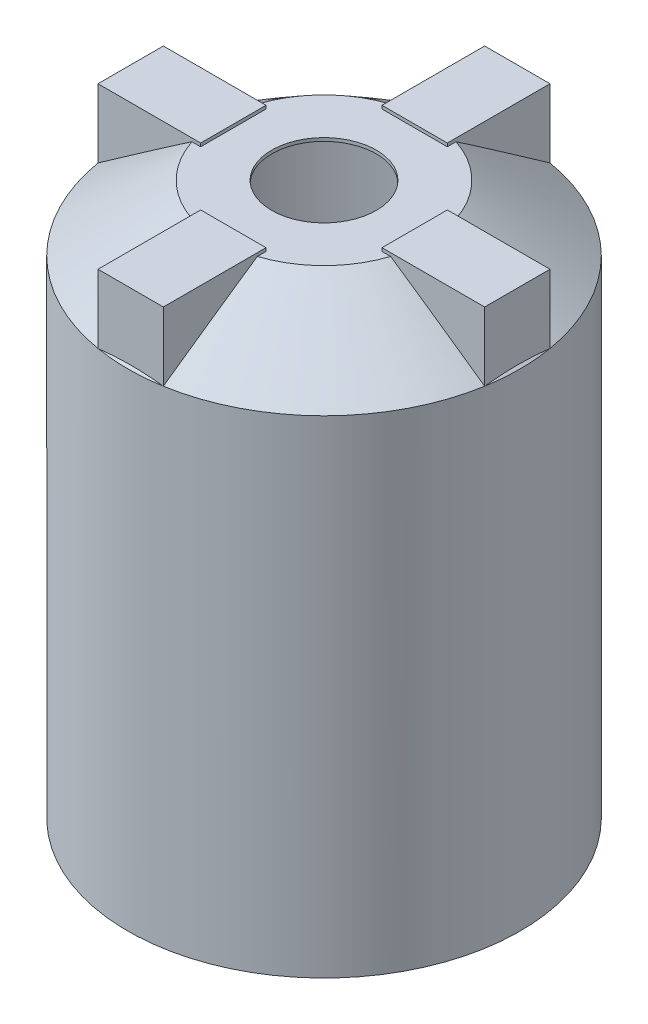
SolidWorks part; units mm, degrees
material "Polyethylene Cross-Linked"
ref_plane "Front Plane" through (0, 0, 0) normal (0, 0, 1) x (1, 0, 0)
ref_plane "Top Plane" through (0, 0, 0) normal (0, 1, 0) x (1, 0, 0)
ref_plane "Right Plane" through (0, 0, 0) normal (1, 0, 0) x (0, 0, -1)
sketch "Sketch1" plane through (0, 0, 0) normal (0, 1, 0) x (1, 0, 0)
  circle A0 centre (0, 0) radius 381
  circle A1 centre (0, 0) radius 374.65
  dimension "D1" = 762
  dimension "D2" = 6.35
extrude "Boss-Extrude1" add sketch "Sketch1" along normal blind 1066.8
sketch "Sketch3" plane through (0, 0, 0) normal (0, 0, 1) x (1, 0, 0)
  line L0 (0, 1066.8) -> (0, 0) construction
  line L2 (203.2, 1066.8) -> (381, 939.8)
  line L3 (381, 1066.8) -> (-381, 1066.8) construction
  line L4 (381, 0) -> (381, 1066.8) construction
  line L8 (374.65, 1066.8) -> (-374.65, 1066.8) construction
  line L9 (201.165, 1060.45) -> (381, 931.9965)
  line L10 (381, 931.9965) -> (381, 939.8)
  line L11 (101.6, 1066.8) -> (101.6, 1060.45)
  line L12 (101.6, 1060.45) -> (201.165, 1060.45)
  line L13 (101.6, 1066.8) -> (203.2, 1066.8)
  point P3 (0, 0)
  point P4 (0, 0)
  point P21 (101.5243, 1066.8)
  dimension "D1" = 203.2
  dimension "D2" = 127
  dimension "D3" = 6.35
  dimension "D4" = 101.6
  dimension "D5" = 6.35
sketch "Sketch4" plane through (0, 1066.8, 0) normal (0, 1, 0) x (1, 0, 0)
  line L0 (63.5, -172.4711) -> (-63.5, -172.4711)
  line L1 (172.4711, 63.5) -> (375.6711, 63.5)
  line L2 (172.4711, 63.5) -> (172.4711, -63.5)
  line L3 (172.4711, -63.5) -> (375.6711, -63.5)
  line L4 (375.6711, 63.5) -> (375.6711, -63.5)
  line L5 (172.4711, 63.5) -> (375.6711, -63.5) construction
  line L6 (172.4711, -63.5) -> (375.6711, 63.5) construction
  line L7 (63.5, -172.4711) -> (63.5, -375.6711)
  line L8 (63.5, -375.6711) -> (-63.5, -375.6711)
  line L9 (-63.5, -172.4711) -> (-63.5, -375.6711)
  line L10 (-172.4711, -63.5) -> (-172.4711, 63.5)
  line L11 (-172.4711, -63.5) -> (-375.6711, -63.5)
  line L12 (-375.6711, -63.5) -> (-375.6711, 63.5)
  line L13 (-172.4711, 63.5) -> (-375.6711, 63.5)
  line L14 (-63.5, 172.4711) -> (63.5, 172.4711)
  line L15 (-63.5, 172.4711) -> (-63.5, 375.6711)
  line L16 (-63.5, 375.6711) -> (63.5, 375.6711)
  line L17 (63.5, 172.4711) -> (63.5, 375.6711)
  circle A2 centre (0, 0) radius 381 construction
  point P0 (274.0711, 0)
  point P5 (0, 0)
  point P6 (-125.3542, -202.3243)
  point P7 (0, 0)
  point P8 (0, 0)
  point P12 (0, 0)
  point P24 (0, 0)
  point P25 (62.648, -375.8141)
  point P26 (-59.9828, 357.5468)
  point P27 (-375.6639, 63.5422)
  point P28 (63.5, -178.9101)
  dimension "D1" = 127
  dimension "D3" = 203.2
  dimension "D2" = 4
revolve "Revolve1" add sketch "Sketch3" angle 360 about L0
sketch "Sketch5" plane through (0, 0, 0) normal (0, 0, 1) x (1, 0, 0)
  line L0 (203.2, 1066.8) -> (381, 939.8)
  line L1 (172.4711, 1066.8) -> (375.6711, 1066.8) construction
  line L2 (203.2, 1066.8) -> (-203.2, 1066.8) construction
  line L3 (381, 0) -> (381, 1066.8) construction
  line L4 (381, 939.8) -> (381, 1066.8)
  line L5 (381, 1066.8) -> (203.2, 1066.8)
  line L6 (0, 0) -> (0, 1066.8) construction
  dimension "D1" = 177.8
  dimension "D2" = 127
revolve "Cut-Revolve2" cut sketch "Sketch5" angle 360 about L6
extrude "Cut-Extrude7" cut sketch "Sketch4" against normal blind 127
sketch "Sketch6" plane through (0, 1066.8, 0) normal (0, 1, 0) x (1, 0, 0)
  line L0 (172.4711, 63.5) -> (172.4711, -63.5) construction
  line L1 (172.4711, 63.5) -> (375.6711, 63.5)
  line L2 (172.4711, 63.5) -> (172.4711, -63.5)
  line L3 (172.4711, -63.5) -> (375.6711, -63.5)
  line L4 (375.6711, 63.5) -> (375.6711, -63.5)
  line L5 (172.4711, 63.5) -> (375.6711, -63.5) construction
  line L6 (172.4711, -63.5) -> (375.6711, 63.5) construction
  line L10 (63.5, -172.4711) -> (-63.5, -172.4711)
  line L11 (182.5176, 57.2209) -> (365.6245, 57.2209)
  line L12 (182.5176, 57.2209) -> (182.5176, -57.2209)
  line L13 (182.5176, -57.2209) -> (365.6245, -57.2209)
  line L14 (365.6245, 57.2209) -> (365.6245, -57.2209)
  line L15 (182.5176, 57.2209) -> (365.6245, -57.2209) construction
  line L16 (182.5176, -57.2209) -> (365.6245, 57.2209) construction
  line L17 (63.5, -172.4711) -> (63.5, -375.6711)
  line L18 (63.5, -375.6711) -> (-63.5, -375.6711)
  line L19 (-63.5, -172.4711) -> (-63.5, -375.6711)
  line L20 (57.2209, -182.5176) -> (-57.2209, -182.5176)
  line L21 (57.2209, -182.5176) -> (57.2209, -365.6245)
  line L22 (57.2209, -365.6245) -> (-57.2209, -365.6245)
  line L23 (-57.2209, -182.5176) -> (-57.2209, -365.6245)
  line L24 (-172.4711, -63.5) -> (-172.4711, 63.5)
  line L25 (-172.4711, -63.5) -> (-375.6711, -63.5)
  line L26 (-375.6711, -63.5) -> (-375.6711, 63.5)
  line L27 (-172.4711, 63.5) -> (-375.6711, 63.5)
  line L28 (-182.5176, -57.2209) -> (-182.5176, 57.2209)
  line L29 (-182.5176, -57.2209) -> (-365.6245, -57.2209)
  line L30 (-365.6245, -57.2209) -> (-365.6245, 57.2209)
  line L31 (-182.5176, 57.2209) -> (-365.6245, 57.2209)
  line L32 (-63.5, 172.4711) -> (63.5, 172.4711)
  line L33 (-63.5, 172.4711) -> (-63.5, 375.6711)
  line L34 (-63.5, 375.6711) -> (63.5, 375.6711)
  line L35 (63.5, 172.4711) -> (63.5, 375.6711)
  line L36 (-57.2209, 182.5176) -> (57.2209, 182.5176)
  line L37 (-57.2209, 182.5176) -> (-57.2209, 365.6245)
  line L38 (-57.2209, 365.6245) -> (57.2209, 365.6245)
  line L39 (57.2209, 182.5176) -> (57.2209, 365.6245)
  line L40 (63.5, 375.6711) -> (63.5, 193.0233) construction
  arc A0 (364.5865, -63.5) -> (364.5865, 63.5) centre (0, 0) ccw construction
  arc A1 (375.6711, 63.5) -> (63.5, 375.6711) centre (0, 0) ccw construction
  point P0 (274.0711, 0)
  point P8 (274.0711, 0)
  point P17 (63.5, 375.6711)
  point P44 (0, 0)
  dimension "D1" = 4
extrude "Boss-Extrude3" add sketch "Sketch6" against normal up to surface (127 mm away) up to face at (-371.5009, 939.8, 0)
sketch "Sketch7" plane through (0, 1066.8, 0) normal (0, 1, 0) x (1, 0, 0)
  line L0 (375.6711, 63.5) -> (193.0233, 63.5) construction
  line L1 (176.1676, 63.5) -> (375.6711, 63.5)
  line L2 (176.1676, 63.5) -> (176.1676, -63.5)
  line L3 (176.1676, -63.5) -> (375.6711, -63.5)
  line L4 (375.6711, 63.5) -> (375.6711, -63.5)
  line L5 (176.1676, 63.5) -> (375.6711, -63.5) construction
  line L6 (176.1676, -63.5) -> (375.6711, 63.5) construction
  line L7 (182.5176, 57.2209) -> (182.5176, -57.2209) construction
  line L8 (63.5, -176.1676) -> (-63.5, -176.1676)
  line L9 (63.5, -176.1676) -> (63.5, -375.6711)
  line L10 (63.5, -375.6711) -> (-63.5, -375.6711)
  line L11 (-63.5, -176.1676) -> (-63.5, -375.6711)
  line L12 (-176.1676, -63.5) -> (-176.1676, 63.5)
  line L13 (-176.1676, -63.5) -> (-375.6711, -63.5)
  line L14 (-375.6711, -63.5) -> (-375.6711, 63.5)
  line L15 (-176.1676, 63.5) -> (-375.6711, 63.5)
  line L16 (-63.5, 176.1676) -> (63.5, 176.1676)
  line L17 (-63.5, 176.1676) -> (-63.5, 375.6711)
  line L18 (-63.5, 375.6711) -> (63.5, 375.6711)
  line L19 (63.5, 176.1676) -> (63.5, 375.6711)
  point P0 (275.9193, 0)
  point P10 (-63.5, 375.6711)
  point P25 (0, 0)
  dimension "D1" = 6.35
  dimension "D2" = 4
extrude "Boss-Extrude4" add sketch "Sketch7" along normal blind 6.35
sketch "Sketch8" plane through (0, 0, 0) normal (0, -1, 0) x (1, 0, 0)
  circle A0 centre (0, 0) radius 381
  circle A1 centre (0, 0) radius 381 construction
extrude "Boss-Extrude5" add sketch "Sketch8" along normal blind 6.35
sketch "Sketch9" plane through (0, 0, 0) normal (0, 0, 1) x (1, 0, 0)
  line L0 (172.4711, 1060.45) -> (374.65, 936.5322)
  line L1 (-374.65, 936.5322) -> (374.65, 936.5322) construction
  line L2 (374.65, 936.5322) -> (172.4711, 936.5322)
  line L3 (172.4711, 939.8) -> (172.4711, 1060.45) construction
  line L4 (172.4711, 936.5322) -> (172.4711, 1060.45)
  line L5 (0, 0) -> (0, 1060.45) construction
  line L6 (-63.5, 1060.45) -> (63.5, 1060.45) construction
  dimension "D1" = 202.1789
revolve "Cut-Revolve3" cut sketch "Sketch9" angle 360 about L5
